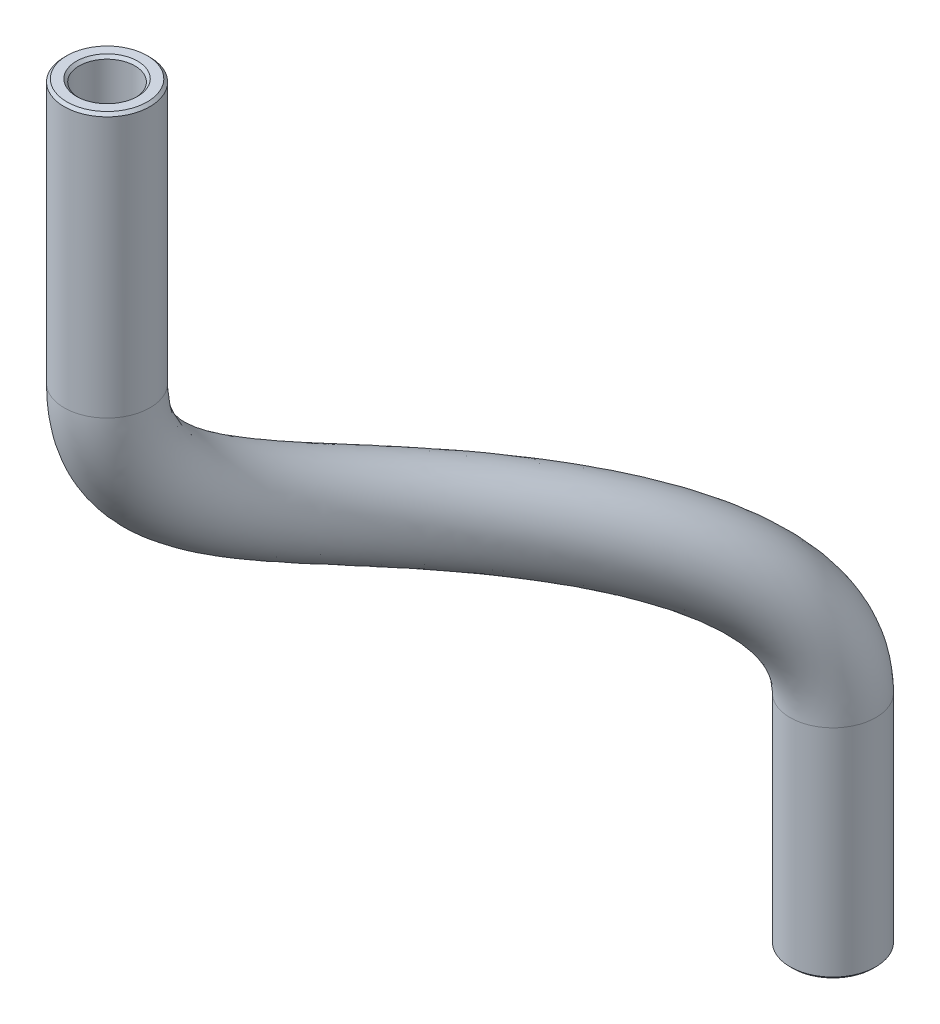
SolidWorks part; units mm, degrees
ref_plane "Front Plane" through (0, 0, 0) normal (0, 0, 1) x (1, 0, 0)
ref_plane "Top Plane" through (0, 0, 0) normal (0, 1, 0) x (1, 0, 0)
ref_plane "Right Plane" through (0, 0, 0) normal (1, 0, 0) x (0, 0, -1)
sketch3d "3DSketch1"
  line L0 (83.325, -62.025, 13.85) -> (83.325, -74.325, 13.85)
  line L1 (93.825, -103.4823, -9.525) -> (93.825, -93.2823, -9.525)
  spline S0 degree 3 poles (83.325, -74.325, 13.85) (83.325, -79.5616, 13.85) (84.1165, -83.7592, 2.1625) (93.825, -87.8292, -9.525) (93.825, -93.2823, -9.525) knots 0 0 0 0 0.49286 1 1 1 1
sketch "Sketch1" plane through (0, -95.3823, 0) normal (0, 1, 0) x (1, 0, 0)
  circle A0 centre (93.825, 9.525) radius 1.3
  circle A1 centre (93.825, 9.525) radius 2
  circle A2 centre (93.825, 9.525) radius 3.6 construction
  dimension "D1" = 2.6
  dimension "D2" = 4
sweep "Sweep1" add profiles "Sketch1" path "3DSketch1"
chamfer "Chamfer1" distance 0.127 angle 45 4 edges at (91.825, -103.4823, -9.525) (92.525, -103.4823, -9.525) (82.5293, -62.025, 15.6849) (82.8078, -62.025, 15.0427)
